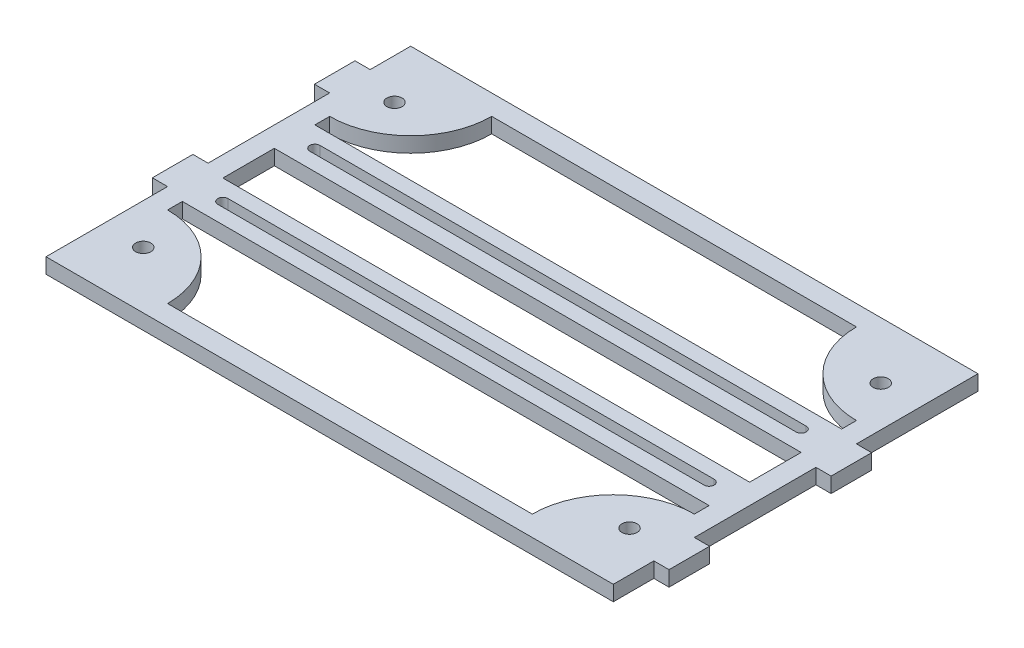
SolidWorks part; units mm, degrees
ref_plane "Front Plane" through (0, 0, 0) normal (0, 0, 1) x (1, 0, 0)
ref_plane "Top Plane" through (0, 0, 0) normal (0, 1, 0) x (1, 0, 0)
ref_plane "Right Plane" through (0, 0, 0) normal (1, 0, 0) x (0, 0, -1)
sketch "Sketch1" plane through (0, 0, 0) normal (0, 1, 0) x (1, 0, 0)
  line L0 (-82.55, -25.4) -> (-82.55, -20.7675)
  line L1 (88.9, -57.15) -> (-88.9, -57.15)
  line L2 (88.9, -57.15) -> (88.9, 57.15)
  line L3 (88.9, 57.15) -> (-88.9, 57.15)
  line L4 (-88.9, -57.15) -> (-88.9, 57.15)
  line L5 (88.9, -57.15) -> (-88.9, 57.15) construction
  line L6 (88.9, 57.15) -> (-88.9, -57.15) construction
  line L7 (57.15, -50.8) -> (-57.15, -50.8)
  line L8 (82.55, -25.4) -> (82.55, -20.7675)
  line L10 (82.55, -20.7675) -> (-82.55, -20.7675)
  line L11 (82.55, -8.0675) -> (-82.55, -8.0675)
  line L12 (0, 0) -> (-76.2, 0) construction
  line L13 (82.55, 8.0675) -> (-82.55, 8.0675)
  line L14 (82.55, 20.7675) -> (-82.55, 20.7675)
  line L15 (-82.55, -8.0675) -> (-82.55, 8.0675)
  line L16 (-82.55, -50.8) -> (-82.55, 50.8) construction
  line L17 (82.55, -8.0675) -> (82.55, 8.0675)
  line L18 (82.55, -50.8) -> (82.55, 50.8) construction
  line L19 (-82.55, 20.7675) -> (-82.55, 25.4)
  line L20 (82.55, 20.7675) -> (82.55, 25.4)
  line L21 (0, 0) -> (0, 34.6317) construction
  line L22 (82.55, 50.8) -> (-82.55, 50.8) construction
  line L23 (82.55, -50.8) -> (-82.55, -50.8) construction
  line L24 (57.15, 50.8) -> (-57.15, 50.8)
  arc A0 (-57.15, -50.8) -> (-82.55, -25.4) centre (-82.55, -50.8) ccw
  arc A1 (57.15, -50.8) -> (82.55, -25.4) centre (82.55, -50.8) cw
  arc A2 (57.15, 50.8) -> (82.55, 25.4) centre (82.55, 50.8) ccw
  arc A3 (-57.15, 50.8) -> (-82.55, 25.4) centre (-82.55, 50.8) cw
  point P0 (0, 0)
  dimension "D6" = 6.35
  dimension "D4" = 25.4
  dimension "D1" = 114.3
  dimension "D2" = 177.8
  dimension "D5" = 12.7
  dimension "D3" = 6.35
extrude "Boss-Extrude1" add sketch "Sketch1" along normal blind 4.7625
sketch "Sketch3" plane through (0, 4.7625, 0) normal (0, 1, 0) x (1, 0, 0)
  line L0 (-76.2, 14.4175) -> (76.2, 14.4175) construction
  line L1 (-76.2, 16.005) -> (76.2, 16.005)
  line L2 (-76.2, 12.83) -> (76.2, 12.83)
  line L3 (82.55, 20.7675) -> (-82.55, 20.7675) construction
  line L6 (82.55, 8.0675) -> (-82.55, 8.0675) construction
  line L7 (0, 0) -> (40.1052, 0) construction
  line L8 (-76.2, -14.4175) -> (76.2, -14.4175) construction
  line L9 (-76.2, -16.005) -> (76.2, -16.005)
  line L10 (-76.2, -12.83) -> (76.2, -12.83)
  arc A0 (-76.2, 16.005) -> (-76.2, 12.83) centre (-76.2, 14.4175) ccw
  arc A1 (76.2, 12.83) -> (76.2, 16.005) centre (76.2, 14.4175) ccw
  arc A2 (-76.2, -16.005) -> (-76.2, -12.83) centre (-76.2, -14.4175) cw
  arc A3 (76.2, -12.83) -> (76.2, -16.005) centre (76.2, -14.4175) cw
  point P2 (0, 14.4175)
  point P11 (0, 8.0675)
  point P17 (0, -14.4175)
  dimension "D1" = 1.5875
  dimension "D2" = 6.35
  dimension "D3" = 152.4
extrude "Cut-Extrude1" cut sketch "Sketch3" against normal through all
sketch "Sketch4" plane through (0, 4.7625, 0) normal (0, 1, 0) x (1, 0, 0)
  line L0 (88.9, 57.15) -> (-88.9, 57.15) construction
  line L2 (0, 0) -> (0, 32.076) construction
  line L3 (0, 0) -> (41.2704, 0) construction
  circle A0 centre (-76.2, 39.37) radius 2.3813
  circle A1 centre (-76.2, -39.37) radius 2.3813
  circle A2 centre (76.2, -39.37) radius 2.3813
  circle A3 centre (76.2, 39.37) radius 2.3813
  arc A4 (-76.2, 16.005) -> (-76.2, 12.83) centre (-76.2, 14.4175) ccw construction
  arc A5 (-76.2, 16.005) -> (-76.2, 12.83) centre (-76.2, 14.4175) ccw
  dimension "D1" = 4.7625
  dimension "D2" = 17.78
extrude "Cut-Extrude2" cut sketch "Sketch4" against normal through all contours A1 | A0 | A3 | A2
hole_wizard "#6-32 Tapped Hole1" positions "Sketch5" profile "Sketch6" tap size "#6-32" standard "Ansi Inch"
sketch "Sketch5" plane through (0, 6.2865, 0) normal (0, 1, 0) x (-1, 0, 0)
  line L2 (0, 0) -> (0, 35.5851) construction
  line L4 (0, 0) -> (43.0458, 0) construction
  point P0 (57.785, -47.625)
  point P15 (57.785, 47.625)
  point P16 (-57.785, 47.625)
  point P17 (-57.785, -47.625)
sketch "Sketch6" plane through (-57.785, 6.2865, -47.625) normal (1, 0, 0) x (0, 0, 1)
  line L0 (0, 0) -> (0, 6.2865)
  line L1 (0, 6.2865) -> (1.3525, 6.2865)
  line L2 (1.3525, 6.2865) -> (1.3525, 0)
  line L3 (1.3525, 0) -> (0, 0)
  line L4 (0, -6.35) -> (0, 107.95) construction
  dimension "Thru Tap Drill Dia." = 2.7051
  dimension "Thru Tap Drill Depth" = 6.2865
cosmetic thread "Hole Thread1" [suppressed]
cosmetic thread "Hole Thread2" [suppressed]
cosmetic thread "Hole Thread3" [suppressed]
cosmetic thread "Hole Thread4" [suppressed]
sketch "Sketch7" plane through (88.9, 0, 0) normal (1, 0, 0) x (0, 0, -1)
  line L0 (-57.15, 2.3813) -> (57.15, 2.3813) construction
  line L1 (-57.15, 4.7625) -> (-57.15, 0) construction
  line L2 (57.15, 4.7625) -> (57.15, 0) construction
  line L4 (-31.75, 4.7625) -> (-44.45, 4.7625)
  line L5 (-31.75, 4.7625) -> (-31.75, 0)
  line L6 (-31.75, 0) -> (-44.45, 0)
  line L7 (-44.45, 4.7625) -> (-44.45, 0)
  line L8 (-31.75, 4.7625) -> (-44.45, 0) construction
  line L9 (-31.75, 0) -> (-44.45, 4.7625) construction
  line L10 (19.05, 4.7625) -> (6.35, 4.7625)
  line L11 (19.05, 4.7625) -> (19.05, 0)
  line L12 (19.05, 0) -> (6.35, 0)
  line L13 (6.35, 4.7625) -> (6.35, 0)
  line L14 (19.05, 4.7625) -> (6.35, 0) construction
  line L15 (19.05, 0) -> (6.35, 4.7625) construction
  point P6 (-38.1, 2.3813)
  point P11 (12.7, 2.3813)
  dimension "D1" = 12.7
  dimension "D2" = 12.7
  dimension "D3" = 19.05
  dimension "D4" = 50.8
  dimension "D5" = 4.7625
  dimension "D6" = 4.7625
extrude "Boss-Extrude2" add sketch "Sketch7" along normal blind 4.7625
sketch "Sketch8" plane through (-88.9, 0, 0) normal (-1, 0, 0) x (0, 0, 1)
  line L0 (-57.15, 2.3813) -> (57.15, 2.3813) construction
  line L1 (-57.15, 4.7625) -> (-57.15, 0) construction
  line L2 (57.15, 4.7625) -> (57.15, 0) construction
  line L4 (-31.75, 4.7625) -> (-44.45, 4.7625)
  line L5 (-31.75, 4.7625) -> (-31.75, 0)
  line L6 (-31.75, 0) -> (-44.45, 0)
  line L7 (-44.45, 4.7625) -> (-44.45, 0)
  line L8 (-31.75, 4.7625) -> (-44.45, 0) construction
  line L9 (-31.75, 0) -> (-44.45, 4.7625) construction
  line L10 (19.05, 4.7625) -> (6.35, 4.7625)
  line L11 (19.05, 4.7625) -> (19.05, 0)
  line L12 (19.05, 0) -> (6.35, 0)
  line L13 (6.35, 4.7625) -> (6.35, 0)
  line L14 (19.05, 4.7625) -> (6.35, 0) construction
  line L15 (19.05, 0) -> (6.35, 4.7625) construction
  point P6 (-38.1, 2.3813)
  point P11 (12.7, 2.3813)
  dimension "D1" = 19.05
  dimension "D2" = 12.7
  dimension "D3" = 50.8
  dimension "D4" = 4.7625
  dimension "D5" = 12.7
  dimension "D6" = 4.7625
extrude "Boss-Extrude3" add sketch "Sketch8" along normal blind 4.7625
equation "\"D2@Sketch3\" = \"D5@Sketch1\"/2"
